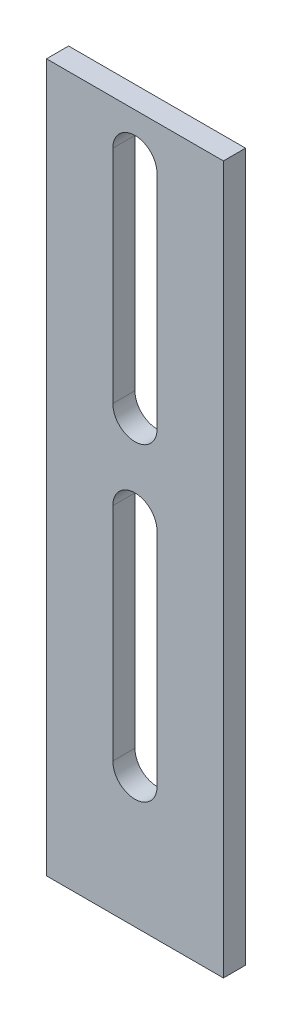
SolidWorks part; units mm, degrees
material "Plain Carbon Steel"
ref_plane "Front Plane" through (0, 0, 0) normal (0, 0, 1) x (1, 0, 0)
ref_plane "Top Plane" through (0, 0, 0) normal (0, 1, 0) x (1, 0, 0)
ref_plane "Right Plane" through (0, 0, 0) normal (1, 0, 0) x (0, 0, -1)
sketch "Sketch1" plane through (0, 0, 0) normal (0, 0, 1) x (1, 0, 0)
  line L0 (12.7, 0) -> (-12.7, 0) construction
  line L1 (-12.7, 12.7) -> (12.7, 12.7)
  line L2 (-12.7, 12.7) -> (-12.7, -88.9)
  line L3 (-12.7, -88.9) -> (12.7, -88.9)
  line L4 (12.7, 12.7) -> (12.7, -88.9)
  line L5 (12.7, -76.2) -> (-12.7, -76.2) construction
  circle A0 centre (0, 6.35) radius 2.3813
  circle A1 centre (0, -69.85) radius 2.3812
  dimension "D9" = 4.7625
  dimension "D10" = 12.7
  dimension "D1" = 25.4
  dimension "D2" = 101.6
  dimension "D3" = 12.7
  dimension "D4" = 12.7
  dimension "D5" = 6.35
  dimension "D6" = 19.05
  dimension "D7" = 12.7
  dimension "D8" = 12.7
  dimension "D11" = 82.55
extrude "Boss-Extrude1" add sketch "Sketch1" along normal blind 3.175
sketch "Sketch2" plane through (0, 0, 3.175) normal (0, 0, 1) x (1, 0, 0)
  line L0 (0, -25.4) -> (0, 6.35) construction
  line L1 (-3.175, -25.4) -> (-3.175, 6.35)
  line L2 (3.175, -25.4) -> (3.175, 6.35)
  line L3 (0, -69.85) -> (0, -38.1) construction
  line L4 (-3.175, -69.85) -> (-3.175, -38.1)
  line L5 (3.175, -69.85) -> (3.175, -38.1)
  line L6 (-12.7, -88.9) -> (12.7, -88.9) construction
  line L7 (12.7, 12.7) -> (-12.7, 12.7) construction
  arc A0 (-3.175, -25.4) -> (3.175, -25.4) centre (0, -25.4) ccw
  arc A1 (3.175, 6.35) -> (-3.175, 6.35) centre (0, 6.35) ccw
  arc A2 (-3.175, -69.85) -> (3.175, -69.85) centre (0, -69.85) ccw
  arc A3 (3.175, -38.1) -> (-3.175, -38.1) centre (0, -38.1) ccw
  circle A4 centre (0, -69.85) radius 2.3812 construction
  point P3 (0, -9.525)
  point P11 (0, -53.975)
  dimension "D1" = 6.35
  dimension "D2" = 6.35
  dimension "D3" = 50.8
  dimension "D4" = 38.1
extrude "Cut-Extrude1" cut sketch "Sketch2" against normal through all
